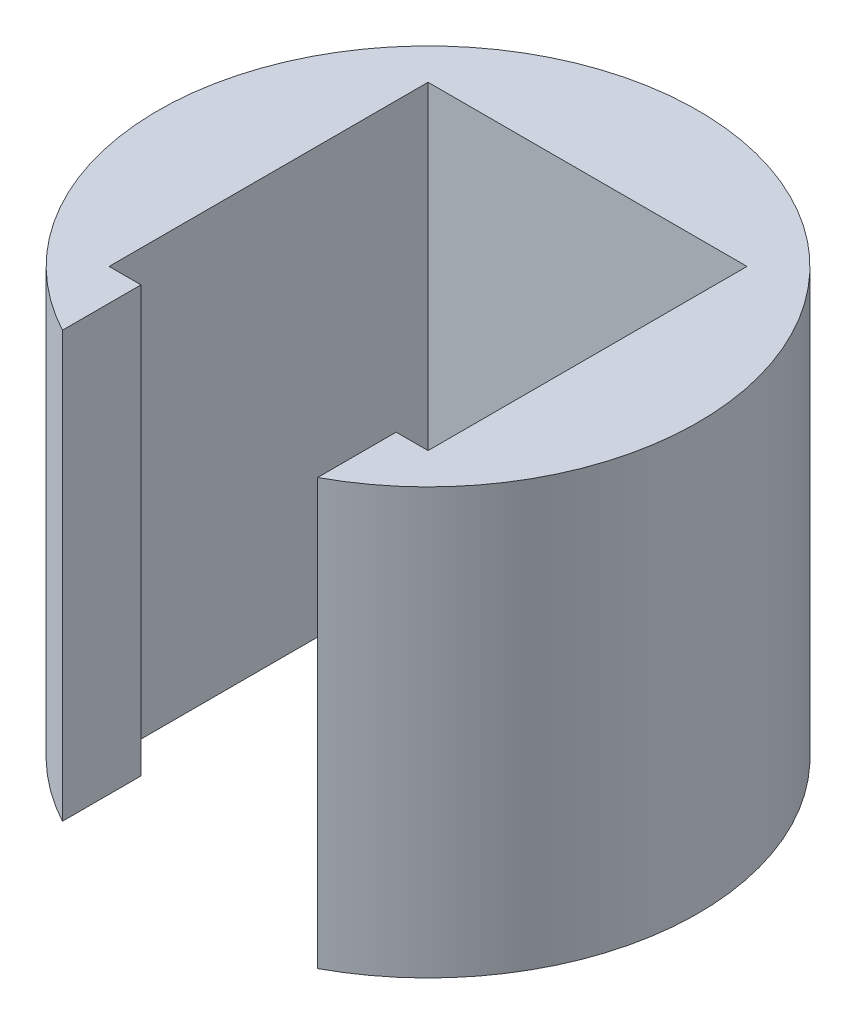
SolidWorks part; units mm, degrees
ref_plane "Front Plane" through (0, 0, 0) normal (0, 0, 1) x (1, 0, 0)
ref_plane "Top Plane" through (0, 0, 0) normal (0, 1, 0) x (1, 0, 0)
ref_plane "Right Plane" through (0, 0, 0) normal (1, 0, 0) x (0, 0, -1)
sketch "Sketch1" plane through (0, 0, 0) normal (0, 1, 0) x (1, 0, 0)
  line L0 (5.9996, -7.5) -> (7.5, -7.5)
  line L1 (-7.5, 7.5) -> (7.5, 7.5)
  line L2 (-7.5, 7.5) -> (-7.5, -7.5)
  line L3 (-7.5, -7.5) -> (-5.9996, -7.5)
  line L4 (7.5, 7.5) -> (7.5, -7.5)
  line L5 (-7.5, 7.5) -> (7.5, -7.5) construction
  line L6 (-7.5, -7.5) -> (7.5, 7.5) construction
  line L7 (-5.9996, -7.5) -> (-5.9996, -11.1935)
  line L9 (5.9996, -11.1935) -> (5.9996, -7.5)
  arc A0 (5.9996, -11.1935) -> (-5.9996, -11.1935) centre (0, 0) ccw
extrude "Boss-Extrude2" add sketch "Sketch1" along normal blind 20
